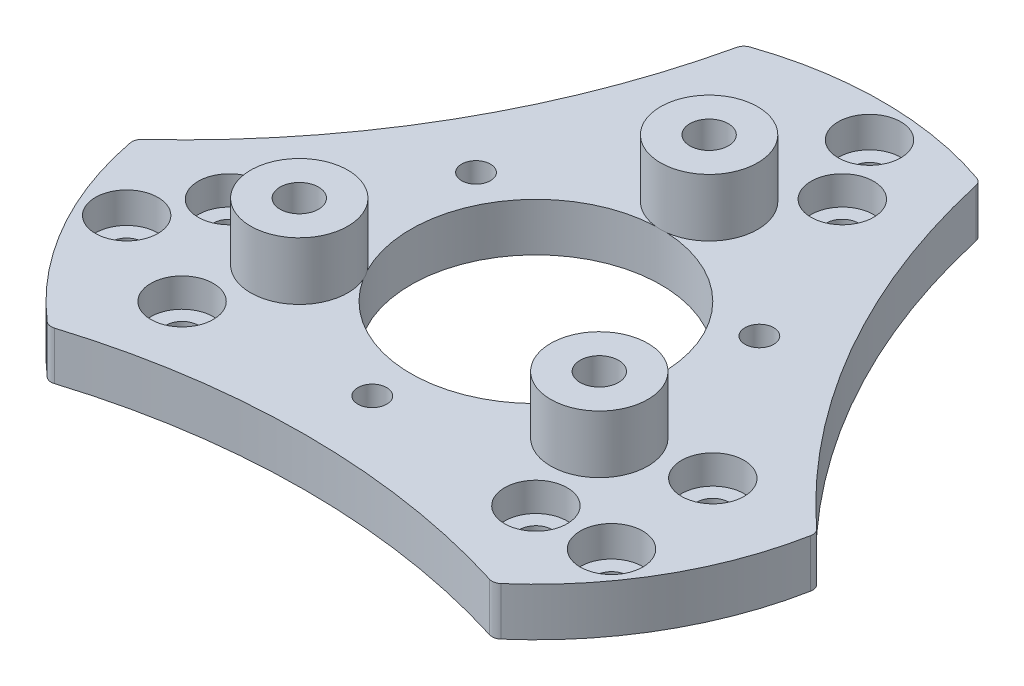
SolidWorks part; units mm, degrees
ref_plane "Front Plane" through (0, 0, 0) normal (0, 0, 1) x (1, 0, 0)
ref_plane "Top Plane" through (0, 0, 0) normal (0, 1, 0) x (1, 0, 0)
ref_plane "Right Plane" through (0, 0, 0) normal (1, 0, 0) x (0, 0, -1)
sketch "Sketch1" plane through (0, 0, 0) normal (0, 1, 0) x (1, 0, 0)
  circle A0 centre (0, 0) radius 36
  circle A1 centre (0, 0) radius 13
  dimension "D1" = 72
  dimension "D2" = 26
extrude "Boss-Extrude1" add sketch "Sketch1" along normal blind 5
sketch "Sketch2" plane through (0, 5, 0) normal (0, 1, 0) x (1, 0, 0)
  line L0 (0, -1000) -> (0, 49000) construction
  line L1 (2.789, 31.8782) -> (0, 0) construction
  circle A0 centre (2.789, 31.8782) radius 1.65
  dimension "D1" = 3.3
  dimension "D2" = 32
  dimension "D3" = 5
extrude "Cut-Extrude1" cut sketch "Sketch2" against normal through all
pattern_circular "CirPattern1" count 3 over 360 about axis through (0, 0, 0) along (0, 1, 0) of "Cut-Extrude1"
sketch "Sketch10" plane through (0, 5, 0) normal (0, 1, 0) x (1, 0, 0)
  line L0 (0, 0) -> (17101.0072, 46984.631) construction
  line L1 (0, 0) -> (-17101.0072, 46984.631) construction
  line L2 (0, 0) -> (0, 50000) construction
  line L3 (-9.5766, 26.3114) -> (-12.3127, 33.8289)
  line L4 (9.5766, 26.3114) -> (12.3127, 33.8289)
  line L5 (17.9981, -21.4492) -> (23.1404, -27.5776)
  line L6 (27.5746, -4.8621) -> (35.4531, -6.2513)
  line L7 (-27.5746, -4.8621) -> (-35.4531, -6.2513)
  line L8 (-17.9981, -21.4492) -> (-23.1404, -27.5776)
  arc A0 (-12.3127, 33.8289) -> (12.3127, 33.8289) centre (0, 0) cw
  circle A1 centre (0, 0) radius 36 construction
  arc A2 (-9.5766, 26.3114) -> (9.5766, 26.3114) centre (0, 0) cw
  arc A3 (35.4531, -6.2513) -> (23.1404, -27.5776) centre (0, 0) cw
  arc A4 (27.5746, -4.8621) -> (17.9981, -21.4492) centre (0, 0) cw
  arc A5 (-23.1404, -27.5776) -> (-35.4531, -6.2513) centre (0, 0) cw
  arc A6 (-17.9981, -21.4492) -> (-27.5746, -4.8621) centre (0, 0) cw
  point P26 (0, 0)
  dimension "D1" = 20
  dimension "D2" = 20
  dimension "D3" = 8
  dimension "D4" = 3
sketch "Sketch3" plane through (0, 5, 0) normal (0, 1, 0) x (1, 0, 0)
  line L0 (0, 0) -> (86.6025, 50) construction
  line L1 (-1000, 0) -> (49000, 0) construction
  circle A0 centre (86.6025, 50) radius 76.0295
  dimension "D3" = 100
extrude "Cut-Extrude2" cut sketch "Sketch3" against normal blind 10
pattern_circular "CirPattern2" count 3 over 360 about axis through (0, 0, 0) along (0, 1, 0) of "Cut-Extrude2"
fillet "Fillet1" radius 1 6 edges at (23.1404, 2.5, 27.5776) (-23.1404, 2.5, 27.5776) (-35.4531, 2.5, 6.2513) (-12.3127, 2.5, -33.8289) (12.3127, 2.5, -33.8289) (35.4531, 2.5, 6.2513)
sketch "Sketch4" plane through (0, 5, 0) normal (0, 1, 0) x (1, 0, 0)
  circle A0 centre (0, 0) radius 6 construction
  circle A1 centre (0, 18) radius 12 construction
  circle A2 centre (0, 18) radius 5.05
  dimension "D1" = 12
  dimension "D2" = 24
  dimension "D3" = 10.1
extrude "Boss-Extrude2" add sketch "Sketch4" along normal blind 6
sketch "Sketch7" plane through (0, 5, 0) normal (0, 1, 0) x (1, 0, 0)
  circle A0 centre (2.789, 31.8782) radius 3.25
  dimension "D1" = 6.5
extrude "Cut-Extrude5" cut sketch "Sketch7" against normal blind 3.2
pattern_circular "CirPattern3" count 3 over 360 about axis through (0, 0, 0) along (0, 1, 0) of "Cut-Extrude5", "Boss-Extrude2"
sketch "Sketch8" plane through (0, 5, 0) normal (0, 1, 0) x (1, 0, 0)
  line L0 (14.7224, 8.5) -> (0, 0) construction
  line L1 (-1000, 0) -> (49000, 0) construction
  circle A0 centre (14.7224, 8.5) radius 1.5
  dimension "D3" = 3
  dimension "D1" = 30
  dimension "D2" = 17
extrude "Cut-Extrude6" cut sketch "Sketch8" against normal blind 10
sketch "Sketch12" plane through (0, 11, 0) normal (0, 1, 0) x (1, 0, 0)
  circle A0 centre (0, 18) radius 2
  dimension "D1" = 4
extrude "Cut-Extrude8" cut sketch "Sketch12" against normal through all
pattern_circular "CirPattern4" count 3 over 360 about axis through (0, 0, 0) along (0, 1, 0) of "Cut-Extrude6", "Cut-Extrude8"
sketch "Sketch9" plane through (0, 5, 0) normal (0, 1, 0) x (1, 0, 0)
  line L0 (-5.7304, 32.4987) -> (0, 0) construction
  line L1 (-25.7839, 33.0244) -> (49214.6038, 8715.4333) construction
  line L2 (-23.1208, 32.4785) -> (49217.2669, 8714.8874) construction
  line L3 (0, -1000) -> (0, 49000) construction
  circle A0 centre (-5.7304, 32.4987) radius 4 construction
  circle A1 centre (-5.7304, 32.4987) radius 1.65
  arc A2 (11.7835, 34.0169) -> (-11.7835, 34.0169) centre (0, 0) ccw construction
  dimension "D1" = 8
  dimension "D2" = 3.3
  dimension "D3" = 1
  dimension "D4" = 10
sketch "Sketch13" plane through (0, 5, 0) normal (0, 1, 0) x (1, 0, 0)
  line L0 (6.7293, 25.1141) -> (0, 0) construction
  line L1 (0, 0) -> (0, 18) construction
  line L2 (-6.7293, 25.1141) -> (0, 0) construction
  circle A0 centre (6.7293, 25.1141) radius 1.7
  circle A1 centre (-6.7293, 25.1141) radius 1.7
  dimension "D1" = 3.4
  dimension "D2" = 26
  dimension "D3" = 15
extrude "Cut-Extrude9" cut sketch "Sketch13" against normal through all
pattern_circular "CirPattern5" count 3 over 360 about axis through (0, 0, 0) along (0, 1, 0) of "Cut-Extrude9"
sketch "Sketch14" plane through (0, 5, 0) normal (0, 1, 0) x (1, 0, 0)
  circle A3 centre (-18.3848, -18.3848) radius 3.25
  circle A4 centre (-25.1141, -6.7293) radius 3.25
  circle A5 centre (-6.7293, 25.1141) radius 3.25
  circle A6 centre (6.7293, 25.1141) radius 3.25
  circle A7 centre (25.1141, -6.7293) radius 3.25
  circle A8 centre (18.3848, -18.3848) radius 3.25
  dimension "D1" = 6.5
extrude "Cut-Extrude10" cut sketch "Sketch14" against normal blind 3
